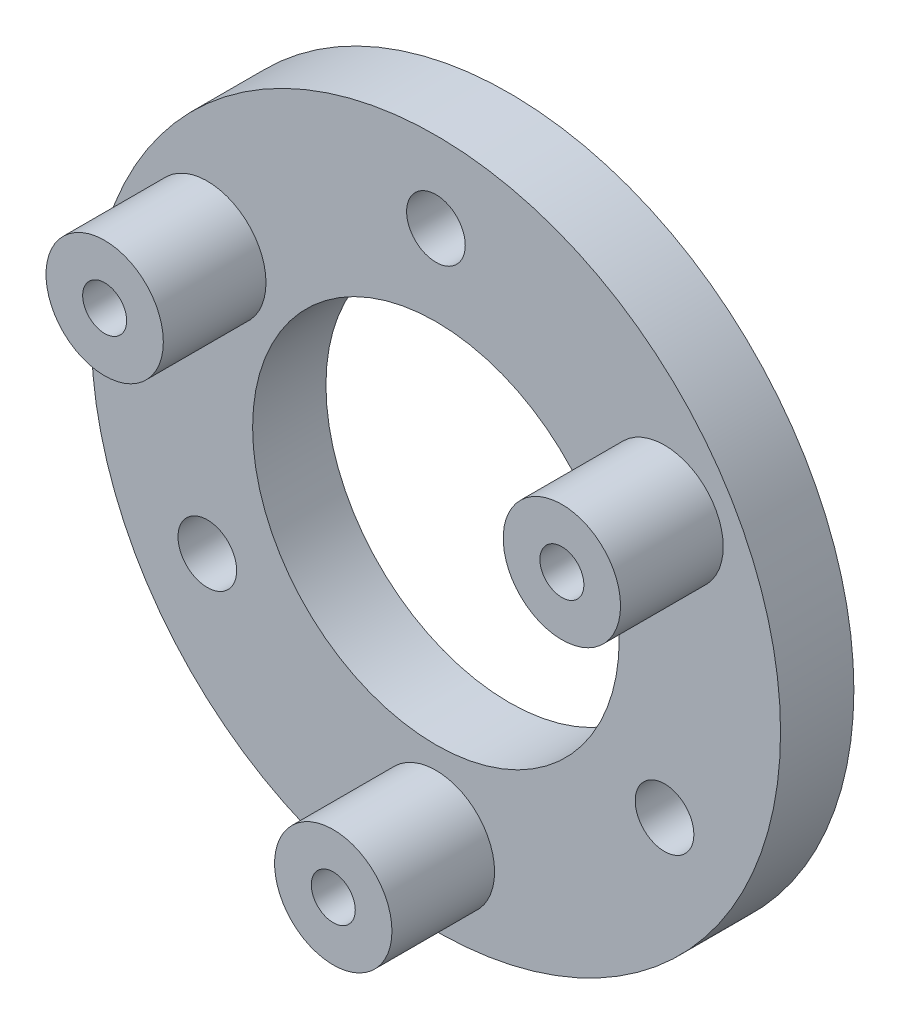
SolidWorks part; units mm, degrees
material "6061 Alloy"
ref_plane "Front Plane" through (0, 0, 0) normal (0, 0, 1) x (1, 0, 0)
ref_plane "Top Plane" through (0, 0, 0) normal (0, 1, 0) x (1, 0, 0)
ref_plane "Right Plane" through (0, 0, 0) normal (1, 0, 0) x (0, 0, -1)
sketch "Sketch1" plane through (0, 0, 0) normal (0, 0, 1) x (1, 0, 0)
  circle A0 centre (0, 0) radius 23.5
  circle A1 centre (0, 0) radius 12.5
  dimension "D1" = 47
  dimension "D2" = 25
extrude "Boss-Extrude1" add sketch "Sketch1" along normal blind 5
sketch "Sketch2" plane through (0, 0, 5) normal (0, 0, 1) x (1, 0, 0)
  circle A0 centre (0, 0) radius 18 construction
  circle A1 centre (0, 18) radius 2
  circle A2 centre (15.5885, -9) radius 2
  circle A3 centre (-15.5885, -9) radius 2
  point P17 (0, 0)
  dimension "D1" = 36
  dimension "D2" = 4
  dimension "D3" = 3
extrude "Cut-Extrude1" cut sketch "Sketch2" against normal blind 3
sketch "Sketch3" plane through (0, 0, 5) normal (0, 0, 1) x (1, 0, 0)
  line L0 (-15.5885, 9) -> (0, 0) construction
  line L1 (0, 18) -> (0, 0) construction
  line L2 (0, 0) -> (-15.5885, -9) construction
  circle A0 centre (0, 0) radius 18 construction
  circle A2 centre (-15.5885, 9) radius 1.5
  circle A3 centre (15.5885, 9) radius 1.5
  circle A4 centre (0, -18) radius 1.5
  point P18 (0, 0)
  dimension "D1" = 36
  dimension "D2" = 3
  dimension "D4" = 60
  dimension "D3" = 3
extrude "Cut-Extrude2" cut sketch "Sketch3" against normal blind 54 and the other way blind 90
sketch "Sketch6" plane through (0, 0, 5) normal (0, 0, 1) x (1, 0, 0)
  circle A0 centre (-15.5885, 9) radius 1.5
  circle A1 centre (-15.5885, 9) radius 4
  circle A2 centre (-15.5885, 9) radius 1.5 construction
  circle A3 centre (15.5885, 9) radius 4
  circle A4 centre (0, -18) radius 4
  circle A6 centre (15.5885, 9) radius 1.5 construction
  circle A7 centre (0, -18) radius 1.5 construction
  circle A8 centre (15.5885, 9) radius 1.5
  circle A9 centre (0, -18) radius 1.5
  point P13 (0, 0)
  dimension "D1" = 8
  dimension "D2" = 3
extrude "Boss-Extrude3" add sketch "Sketch6" along normal blind 7
sketch "Sketch4" plane through (0, 0, 0) normal (0, 0, -1) x (-1, 0, 0)
  line L1 (-13.5677, 5.5) -> (-11.547, 9)
  line L2 (-11.547, 9) -> (-13.5677, 12.5)
  line L3 (-13.5677, 12.5) -> (-17.6092, 12.5)
  line L4 (-17.6092, 12.5) -> (-19.6299, 9)
  line L5 (-19.6299, 9) -> (-17.6092, 5.5)
  line L6 (-17.6092, 5.5) -> (-13.5677, 5.5)
  circle A0 centre (-15.5885, 9) radius 3.5 construction
  dimension "D1" = 7
extrude "Cut-Extrude3" [suppressed] cut sketch "Sketch4" against normal blind 3
pattern_circular "CirPattern1" [suppressed] count 3 over 360
sketch "Sketch7" plane through (0, 0, 12) normal (0, 0, 1) x (1, 0, 0)
  circle A0 centre (-15.5885, 9) radius 4
  circle A2 centre (-15.5885, 9) radius 1.5 construction
  circle A3 centre (-15.5885, 9) radius 1.5
  circle A4 centre (15.5885, 9) radius 4
  circle A5 centre (15.5885, 9) radius 1.5
  circle A6 centre (0, -18) radius 4
  circle A7 centre (0, -18) radius 1.5
  point P18 (0, 0)
  dimension "D1" = 8
  dimension "D2" = 8
  dimension "D3" = 3
extrude "Boss-Extrude4" add sketch "Sketch7" against normal blind 3
fillet "Fillet3" [suppressed] radius 2
fillet "Fillet4" [suppressed] radius 2.5
fillet "Fillet5" [suppressed] radius 2
chamfer "Chamfer3" [suppressed] distance 2 angle 45
fillet "Fillet6" [suppressed] radius 2
sketch "Sketch10" plane through (0, 0, 0) normal (0, 0, -1) x (-1, 0, 0)
  line L1 (-13.8564, 12) -> (-17.3205, 12)
  line L2 (-17.3205, 12) -> (-19.0526, 9)
  line L3 (-19.0526, 9) -> (-17.3205, 6)
  line L4 (-17.3205, 6) -> (-13.8564, 6)
  line L5 (-13.8564, 6) -> (-12.1244, 9)
  line L6 (-12.1244, 9) -> (-13.8564, 12)
  circle A0 centre (-15.5885, 9) radius 3 construction
  dimension "D1" = 6
extrude "Cut-Extrude5" [suppressed] cut sketch "Sketch10" against normal blind 3
pattern_circular "CirPattern2" [suppressed] count 3 over 360
chamfer "Chamfer4" [suppressed] distance 2 angle 45
chamfer "Chamfer5" [suppressed] distance 2 angle 45
sketch "Sketch11" plane through (0, 0, 0) normal (0, 0, -1) x (-1, 0, 0)
  circle A1 centre (0, 0) radius 23.5
  circle A2 centre (0, 0) radius 23.5
  dimension "D1" = 0
extrude "Cut-Extrude6" [suppressed] cut sketch "Sketch11" against normal blind 2
sketch "Sketch12" plane through (0, 0, 5) normal (0, 0, 1) x (1, 0, 0)
  circle A0 centre (0, 0) radius 23.5 construction
  circle A1 centre (0, 0) radius 12.5 construction
  circle A2 centre (0, 0) radius 23.5
  circle A3 centre (0, 0) radius 12.5
extrude "Boss-Extrude5" [suppressed] add sketch "Sketch12" along normal up to surface (7 mm away)
